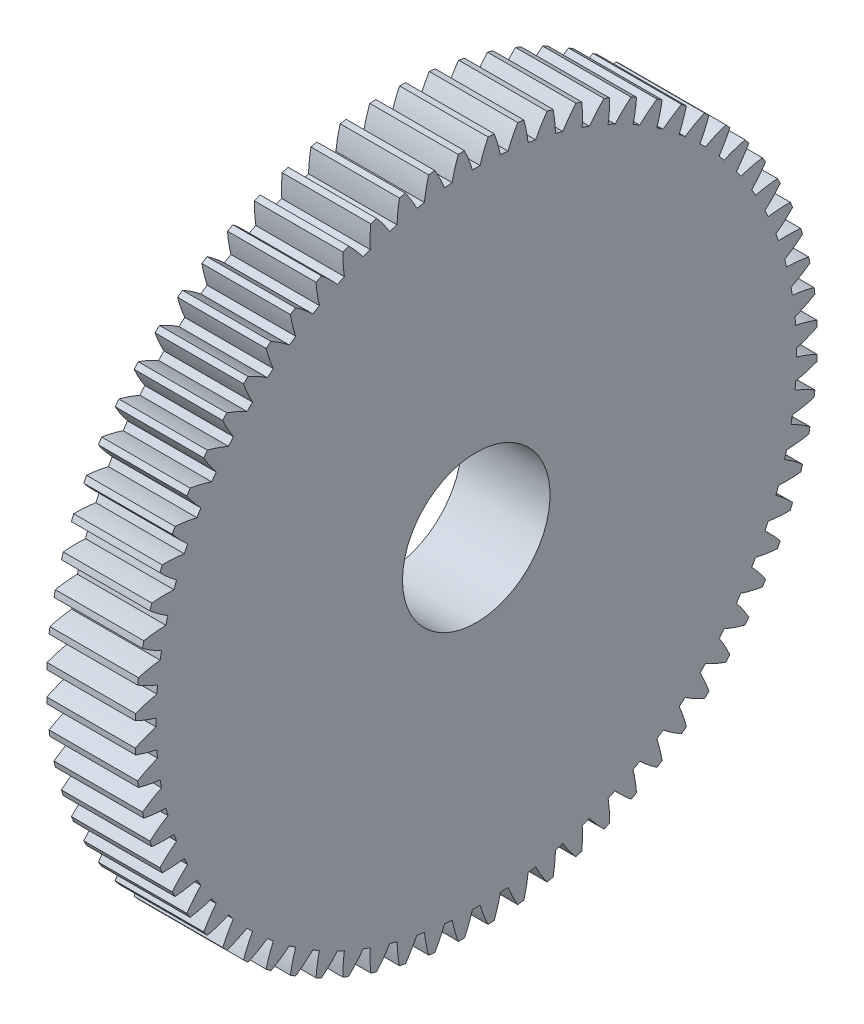
SolidWorks part; units mm, degrees
ref_plane "Plane1" through (0, 0, 0) normal (0, 0, 1) x (1, 0, 0)
ref_plane "Plane2" through (0, 0, 0) normal (0, 1, 0) x (1, 0, 0)
ref_plane "Plane3" through (0, 0, 0) normal (1, 0, 0) x (0, 0, -1)
other "Configuration Table"
sketch "HoldingSke" plane through (0, 0, 0) normal (0, 1, 0) x (1, 0, 0)
  line L0 (0, 0) -> (251.169, -773.0187)
  line L1 (-15, 0) -> (100, 0) construction
  line L2 (0, 0) -> (-2.1039, 2.3779)
  line L3 (0, 0) -> (-11.863, 4.5341)
  line L4 (0, 0) -> (2.6687, 8.2133)
  line L5 (0, 0) -> (-47.5972, -17.7524)
  line L6 (0, 0) -> (-6.3167, -4.2619)
  line L7 (-2.1039, 2.3779) -> (8.8308, 51.9871)
  line L8 (-76.2, 54.61) -> (-61.976, 54.61)
  line L9 (-71.009, 38.7566) -> (-53.1078, 45.2721)
  line L10 (-76.2, 71.12) -> (104.1128, 71.12)
  line L11 (0, 0) -> (-7.62, 0)
  line L12 (-76.2, 101.6) -> (-76.1716, 101.6)
  line L13 (24.9733, 27.94) -> (52.9518, 28.4284)
  line L14 (24.9733, 27.94) -> (25.0241, 27.9398)
  line L15 (24.9733, 27.94) -> (100.4021, 29.52)
  circle A0 centre (0, 0) radius 6.35
  circle A1 centre (0, 0) radius 27.5717
  circle A2 centre (0, 0) radius 38.1
  circle A3 centre (0, 0) radius 6.35
  dimension "MHD" = 55.1434
  dimension "Hub_dia" = 76.2
  dimension "Bore" = 12.7
  dimension "MBD" = 12.7
  dimension "Num_teeth" = 72
  dimension "Pitch" = 812.8
  dimension "Overall_len" = 50.8
  dimension "Show_teeth" = 72
  dimension "Thickness" = 7.62
  dimension "OAL" = 50.8001
  dimension "T_dim" = 14.224
  dimension "Ap" = 20
  dimension "H" = 19.05
  dimension "Pitch_radius" = 180.3128
  dimension "Width" = 7.62
  dimension "Backlash" = 0.0284
  dimension "Addendum_fac" = 1
  dimension "Dedendum_fac" = 1.2
  dimension "Clearance_fac" = 0.2
  dimension "Dedendum_add" = 0.0508
sketch "BasProSke" plane through (0, 0, 0) normal (0, 1, 0) x (1, 0, 0)
  line L0 (-10, 0) -> (60, 0) construction
  line L1 (0, 0) -> (0, 29.3687)
  line L2 (0, 0) -> (7.62, 0)
  line L3 (7.62, 0) -> (7.62, 29.3687)
  line L4 (7.62, 29.3687) -> (0, 29.3687)
  dimension "Thickness" = 7.62
  dimension "Diameter" = 58.7375
revolve "Base-Revolve" add sketch "BasProSke" angle 360 about L0
sketch "TooCutSke" plane through (0, 0, 0) normal (1, 0, 0) x (0, 0, -1)
  line L1 (0, 0) -> (0, 107) construction
  line L2 (0, 0) -> (-0.6731, 28.5671) construction
  line L3 (0, 0) -> (-2.4923, 57.0841) construction
  line L4 (-0.6731, 28.5671) -> (-1.2462, 28.5421) construction
  arc A0 (0.3305, 27.5697) -> (-0.3305, 27.5697) centre (0, 0) ccw
  arc A1 (1.0304, 29.3761) -> (-1.0304, 29.3761) centre (0, 0) ccw
  circle A2 centre (0, 0) radius 28.575 construction
  circle A3 centre (0, 0) radius 26.8517 construction
  arc A4 (-0.3305, 27.5697) -> (-1.0304, 29.3761) centre (-11.3, 24.3582) ccw
  arc A5 (1.0304, 29.3761) -> (0.3305, 27.5697) centre (11.3, 24.3582) ccw
  dimension "Root_dia" = 55.1434
  dimension "Overcut_dia" = 58.7883
  dimension "Pitch_dia" = 57.15
  dimension "Base_dia" = 53.7034
  dimension "Flank_rad" = 11.43
  dimension "Half_ang" = 2.5
  dimension "Half_CT" = 0.5736
extrude "ToothCut" cut sketch "TooCutSke" along normal through all
fillet "Breaks" [suppressed] radius 0.0159
fillet "RootFillets" [suppressed] radius 0.2095
pattern_circular "TeethCuts" count 72 every 5 about axis through (-10, 0, 0) along (1, 0, 0) of "ToothCut", "RootFillets", "Breaks"
sketch "HubNeaOneSke" plane through (0, 0, 0) normal (-1, 0, 0) x (0, 0, 1)
  circle A0 centre (0, 0) radius 27.5717
  dimension "Diameter" = 55.1434
extrude "HubNearOne" [suppressed] add sketch "HubNeaOneSke" along normal blind 43.1801
sketch "HubNeaBotSke" plane through (0, 0, 0) normal (-1, 0, 0) x (0, 0, 1)
  circle A0 centre (0, 0) radius 27.5717
  dimension "Diameter" = 55.1434
extrude "HubNearBoth" [suppressed] add sketch "HubNeaBotSke" along normal blind 21.59
ref_plane "FarPln" through (7.62, 0, 0) normal (1, 0, 0) x (0, 0, -1)
sketch "HubFarSke" plane through (7.62, 0, 0) normal (1, 0, 0) x (0, 0, -1)
  circle A0 centre (0, 0) radius 27.5717
  dimension "Diameter" = 55.1434
extrude "HubFar" [suppressed] add sketch "HubFarSke" along normal blind 21.59
sketch "BorSke" plane through (0, 0, 0) normal (1, 0, 0) x (0, 0, -1)
  circle A0 centre (0, 0) radius 6.35
  dimension "Diameter" = 12.7
extrude "Bore" cut sketch "BorSke" along normal mid plane 101.6001
sketch "KeySke" plane through (0, 0, 0) normal (1, 0, 0) x (0, 0, -1)
  line L0 (-1.5875, 0) -> (-1.5875, 7.874)
  line L1 (-1.5875, 7.874) -> (1.5875, 7.874)
  line L2 (1.5875, 7.874) -> (1.5875, 0)
  line L3 (0, 0) -> (0, 34) construction
  line L4 (-1.5875, 0) -> (1.5875, 0)
  dimension "Offset" = 7.874
  dimension "Width" = 3.175
extrude "Keyway" [suppressed] cut sketch "KeySke" along normal mid plane 101.6001
pattern_circular "Keyway2" [suppressed] count 2 every 90 about axis through (-10, 0, 0) along (1, 0, 0)
equation "' \"Pitch@HoldingSke\" = 4"
equation "' \"Num_teeth@HoldingSke\" = 12"
equation "' \"Ap@HoldingSke\" =  20"
equation "' \"Ap@HoldingSke\" = 20"
equation "' \"Width@HoldingSke\" = 0.5"
equation "' \"Hub_dia@HoldingSke\"= 1"
equation "' \"Hub_dia@HoldingSke\" = 1"
equation "' \"Overall_len@HoldingSke\" = 1.0"
equation "' \"Bore@HoldingSke\" = 0.75"
equation "' \"T_dim@HoldingSke\" = 0.85"
equation "' \"Width@KeySke\" = 0.25"
equation "' \"Show_teeth@HoldingSke\" = 13"
equation "' \"Backlash@HoldingSke\" = 0.009"
equation "' \"Addendum_fac@HoldingSke\" = 1.0"
equation "' \"Dedendum_fac@HoldingSke\" = 1.25"
equation "' \"Dedendum_add@HoldingSke\" = 0.00005"
equation "' \"Clearance_fac@HoldingSke\" = 0.25"
equation "' \"Pitch@HoldingSke\" = 0.5"
equation "' \"Num_teeth@HoldingSke\" = 23"
equation "' \"Show_teeth@HoldingSke\" = 23"
equation "' \"Backlash@HoldingSke\" = 0.0375"
equation "\"Overcut_dia@TooCutSke\" = (\"Num_teeth@HoldingSke\" + 2 * \"Addendum_fac@HoldingSke\") / \"Pitch@HoldingSke\" + 0.002"
equation "\"Pitch_dia@TooCutSke\" = \"Num_teeth@HoldingSke\" / \"Pitch@HoldingSke\""
equation "\"Base_dia@TooCutSke\" = \"Num_teeth@HoldingSke\" / \"Pitch@HoldingSke\" * cos((\"Ap@HoldingSke\"  * 3.14159265 / 180))"
equation "\"Root_dia@TooCutSke\" = (\"Num_teeth@HoldingSke\" + 2) / \"Pitch@HoldingSke\" - 2 * (\"Addendum_fac@HoldingSke\" + \"Dedendum_fac@HoldingSke\") / \"Pitch@HoldingSke\" - \"Dedendum_add@HoldingSke\" * 2"
equation "\"Half_ang@TooCutSke\" = 180 / \"Num_teeth@HoldingSke\""
equation "\"Half_CT@TooCutSke\" = \"Num_teeth@HoldingSke\" / \"Pitch@HoldingSke\" * sin((3.14159265 / 2 / \"Num_teeth@HoldingSke\")) / 2 - 7 * \"Backlash@HoldingSke\" / 4"
equation "\"Flank_rad@TooCutSke\" = \"Num_teeth@HoldingSke\" / \"Pitch@HoldingSke\" / 5"
equation "\"Radius@RootFillets\" = \"Clearance_fac@HoldingSke\" / \"Pitch@HoldingSke\" + \"Dedendum_add@HoldingSke\""
equation "\"Break_rad@Breaks\" = 0.02 / \"Pitch@HoldingSke\""
equation "\"Thickness@HoldingSke\" = \"Width@HoldingSke\""
equation "\"OAL@HoldingSke\" = \"Thickness@HoldingSke\""
equation "\"MHD@HoldingSke\" = (\"Num_teeth@HoldingSke\" + 2) / \"Pitch@HoldingSke\" - 2 * (\"Addendum_fac@HoldingSke\" + \"Dedendum_fac@HoldingSke\")  / \"Pitch@HoldingSke\" - \"Dedendum_add@HoldingSke\" * 2"
equation "\"MBD@HoldingSke\" = (\"Num_teeth@HoldingSke\" + 2) / \"Pitch@HoldingSke\" - 2 * (\"Addendum_fac@HoldingSke\" + \"Dedendum_fac@HoldingSke\")  / \"Pitch@HoldingSke\" - \"Dedendum_add@HoldingSke\" * 2 - 0.002"
equation "\"MHD@HoldingSke\" = ((sgn( \"MHD@HoldingSke\" - \"Hub_dia@HoldingSke\" )-1)*( \"MHD@HoldingSke\" - \"Hub_dia@HoldingSke\" ))/-2+ \"Hub_dia@HoldingSke\""
equation "\"MBD@HoldingSke\" = ((sgn( \"MBD@HoldingSke\" - \"Bore@HoldingSke\" )-1)*( \"MBD@HoldingSke\" - \"Bore@HoldingSke\" ))/-2+ \"Bore@HoldingSke\""
equation "\"OAL@HoldingSke\" = ((sgn( \"OAL@HoldingSke\" - \"Overall_len@HoldingSke\" )+1)*( \"OAL@HoldingSke\" - \"Overall_len@HoldingSke\" ))/2 + \"Overall_len@HoldingSke\" + 0.000002"
equation "\"Num_teeth@TeethCuts\" = int( \"Show_teeth@HoldingSke\" ) + 1"
equation "\"Num_teeth@TeethCuts\" = ((sgn( \"Num_teeth@TeethCuts\" - \"Num_teeth@HoldingSke\" )-1)*( \"Num_teeth@TeethCuts\" - \"Num_teeth@HoldingSke\" ))/-2+ \"Num_teeth@HoldingSke\""
equation "\"Num_teeth@TeethCuts\" = ((sgn( \"Num_teeth@TeethCuts\" - 2.0)+1)*( \"Num_teeth@TeethCuts\" - 2.0))/2 +2.0"
equation "\"Angle@TeethCuts\" = 360.0 / \"Num_teeth@HoldingSke\""
equation "\"Diameter@BasProSke\" = (\"Num_teeth@HoldingSke\" + 2 * \"Addendum_fac@HoldingSke\") / \"Pitch@HoldingSke\""
equation "\"Thickness@BasProSke\"  = \"Thickness@HoldingSke\""
equation "' \"Fillet_rad@BasProSke\" =  \"Thickness@HoldingSke\" * 0.05"
equation "' \"Fillet_rad@BasProSke\" = \"Thickness@HoldingSke\" * 0.05"
equation "\"MHD@HoldingSke\" = ((sgn( \"MHD@HoldingSke\" - \"Root_dia@TooCutSke\" )-1)*( \"MHD@HoldingSke\" - \"Root_dia@TooCutSke\" ))/-2+ \"Root_dia@TooCutSke\""
equation "\"Diameter@HubNeaOneSke\" = \"MHD@HoldingSke\""
equation "\"Length@HubNearOne\" = \"OAL@HoldingSke\" - \"Thickness@BasProSke\""
equation "\"Diameter@HubNeaBotSke\" = \"MHD@HoldingSke\""
equation "\"Length@HubNearBoth\" = ( \"OAL@HoldingSke\" - \"Thickness@BasProSke\" ) / 2.0"
equation "\"Thickness@FarPln\" = \"Thickness@BasProSke\""
equation "\"Diameter@HubFarSke\" = \"MHD@HoldingSke\""
equation "\"Length@HubFar\" = ( \"OAL@HoldingSke\" - \"Thickness@BasProSke\" ) / 2.0"
equation "\"Diameter@BorSke\" = \"MBD@HoldingSke\""
equation "\"D1@Bore\" = \"OAL@HoldingSke\" * 2.0"
equation "\"D1@Keyway\" = \"OAL@HoldingSke\" * 2.0"
equation "\"Offset@KeySke\" = \"T_dim@HoldingSke\" - \"MBD@HoldingSke\" / 2.0"
